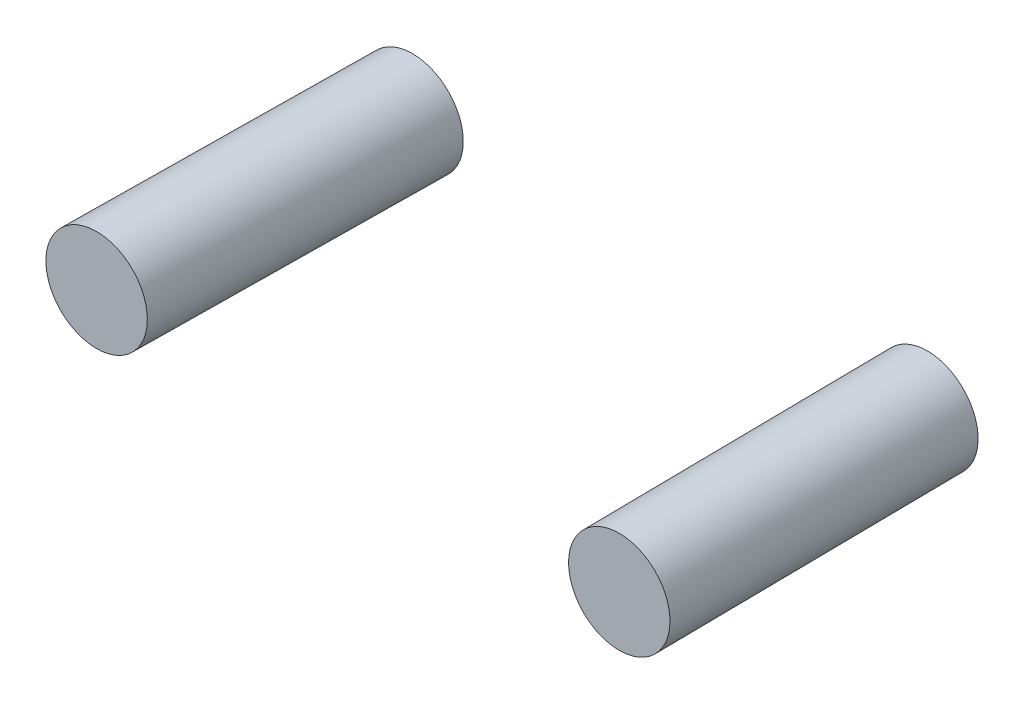
SolidWorks part; units mm, degrees
ref_plane "Front Plane" through (0, 0, 0) normal (0, 0, 1) x (1, 0, 0)
ref_plane "Top Plane" through (0, 0, 0) normal (0, 1, 0) x (1, 0, 0)
ref_plane "Right Plane" through (0, 0, 0) normal (1, 0, 0) x (0, 0, -1)
sketch "Sketch1" plane through (0, 0, 0) normal (0, 1, 0) x (1, 0, 0)
  line L0 (-83.82, 101.6) -> (-85.09, 0)
  line L1 (-85.09, 0) -> (0, 0) construction
  line L2 (0, 0) -> (0, 101.6) construction
  line L3 (0, 101.6) -> (-83.82, 101.6) construction
  dimension "D1" = 83.82
  dimension "D2" = 85.09
  dimension "D3" = 101.6
sketch "Sketch2" plane through (0, 0, 0) normal (0, 0, 1) x (1, 0, 0)
  line L0 (-85.09, 0) -> (0, 0) construction
  circle A0 centre (-85.09, 0) radius 16.51
  point P4 (-150.8049, 0)
  point P5 (0, 0)
  dimension "D1" = 33.02
sweep "Sweep1" add profiles "Sketch2" path "Sketch1"
mirror "Mirror3" about plane through (0, 0, 0) normal (1, 0, 0) of bodies 101
